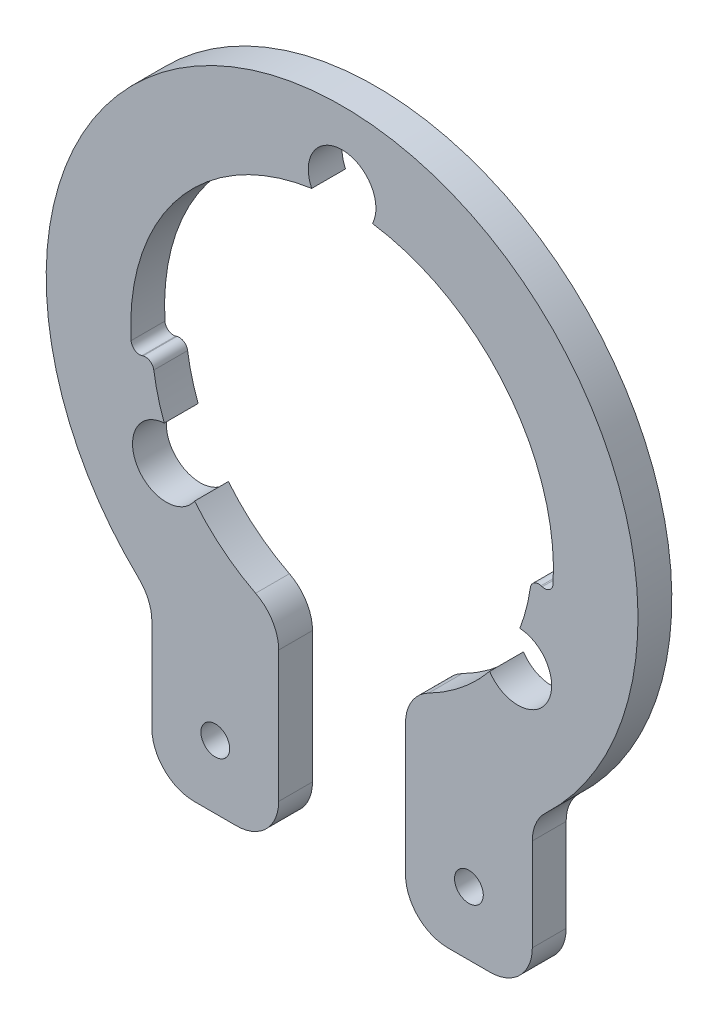
SolidWorks part; units mm, degrees
ref_plane "Front Plane" through (0, 0, 0) normal (0, 0, 1) x (1, 0, 0)
ref_plane "Top Plane" through (0, 0, 0) normal (0, 1, 0) x (1, 0, 0)
ref_plane "Right Plane" through (0, 0, 0) normal (1, 0, 0) x (0, 0, -1)
sketch "Sketch2" plane through (0, 0, 0) normal (0, 0, 1) x (1, 0, 0)
  line L0 (0, 63.6483) -> (0, -57.393) construction
  line L1 (0, 0) -> (-20.7846, -12) construction
  circle A0 centre (0, 0) radius 20 construction
  circle A1 centre (0, 0) radius 22.5 construction
  circle A2 centre (0, 26.5) radius 4
  circle A3 centre (-20.7846, -12) radius 4
  circle A4 centre (20.7846, -12) radius 4
  dimension "D1" = 40
  dimension "D2" = 45
  dimension "D4" = 8
  dimension "D3" = 60
sketch "Sketch3" plane through (0, 0, 0) normal (0, 0, 1) x (1, 0, 0)
  line L0 (-7.5, -21.2132) -> (-7.5, -45)
  line L1 (-7.5, -45) -> (-22.5, -45)
  line L2 (-22.5, -45) -> (-22.5, -26.8095)
  line L3 (22.5, -45) -> (22.5, -26.8095)
  line L5 (0, 36.5) -> (0, 40) construction
  line L6 (7.5, -45) -> (22.5, -45)
  line L7 (7.5, -21.2132) -> (7.5, -45)
  arc A0 (7.5, -21.2132) -> (22.3988, -2.1311) centre (0, 0) ccw
  arc A1 (-22.3988, -2.1311) -> (-24.8362, -2.8575) centre (-20.7846, -12) ccw
  arc A2 (22.3988, -2.1311) -> (24.8362, -2.8575) centre (20.7846, -12) cw
  circle A3 centre (0, 0) radius 22.5 construction
  arc A4 (-7.5, -21.2132) -> (-22.3988, -2.1311) centre (0, 0) cw
  arc A6 (22.5, -26.8095) -> (-22.5, -26.8095) centre (0, 0) ccw
  arc A7 (24.8362, -2.8575) -> (-24.8362, -2.8575) centre (0, 0) ccw
  point P0 (0, 26.5)
  point P1 (-20.7846, -12)
  dimension "D1" = 25
  dimension "D2" = 35
  dimension "D3" = 10
  dimension "D4" = 45
  dimension "D5" = 15
  dimension "D6" = 45
extrude "Boss-Extrude1" add sketch "Sketch3" along normal blind 4
extrude "Cut-Extrude2" cut sketch "Sketch2" along normal through all
sketch "Sketch4" [suppressed] plane through (0, 0, 0) normal (0, 0, 1) x (1, 0, 0)
  line L1 (-9, -20.6216) -> (-9, -41.129)
  line L2 (-9, -41.129) -> (9, -41.129)
  line L3 (9, -41.129) -> (9, -20.6216)
  arc A0 (9, -20.6216) -> (-9, -20.6216) centre (0, 0) cw
  arc A1 (-17.448, -14.2062) -> (-9, -20.6216) centre (0, 0) ccw construction
extrude "Boss-Extrude2" [suppressed] add sketch "Sketch4" along normal up to surface (4 mm away)
sketch "Sketch5" plane through (0, 0, 0) normal (0, 0, 1) x (1, 0, 0)
  line L0 (0, 0) -> (0, -43.3189) construction
  circle A0 centre (-15, -37.5) radius 1.7
  circle A1 centre (15, -37.5) radius 1.7
  dimension "D1" = 3.4
  dimension "D2" = 30
  dimension "D3" = 37.5
extrude "Cut-Extrude3" cut sketch "Sketch5" along normal through all
fillet "Fillet1" radius 5 2 edges at (22.5, -45, 2) (-22.5, -45, 2)
fillet "Fillet2" radius 5 6 edges at (7.5, -45, 2) (7.5, -21.2132, 2) (-7.5, -45, 2) (-7.5, -21.2132, 2) (22.5, -26.8095, 2) (-22.5, -26.8095, 2)
fillet "Fillet3" radius 1 4 edges at (-24.8362, -2.8575, 2) (-22.3988, -2.1311, 2) (24.8362, -2.8575, 2) (22.3988, -2.1311, 2)
